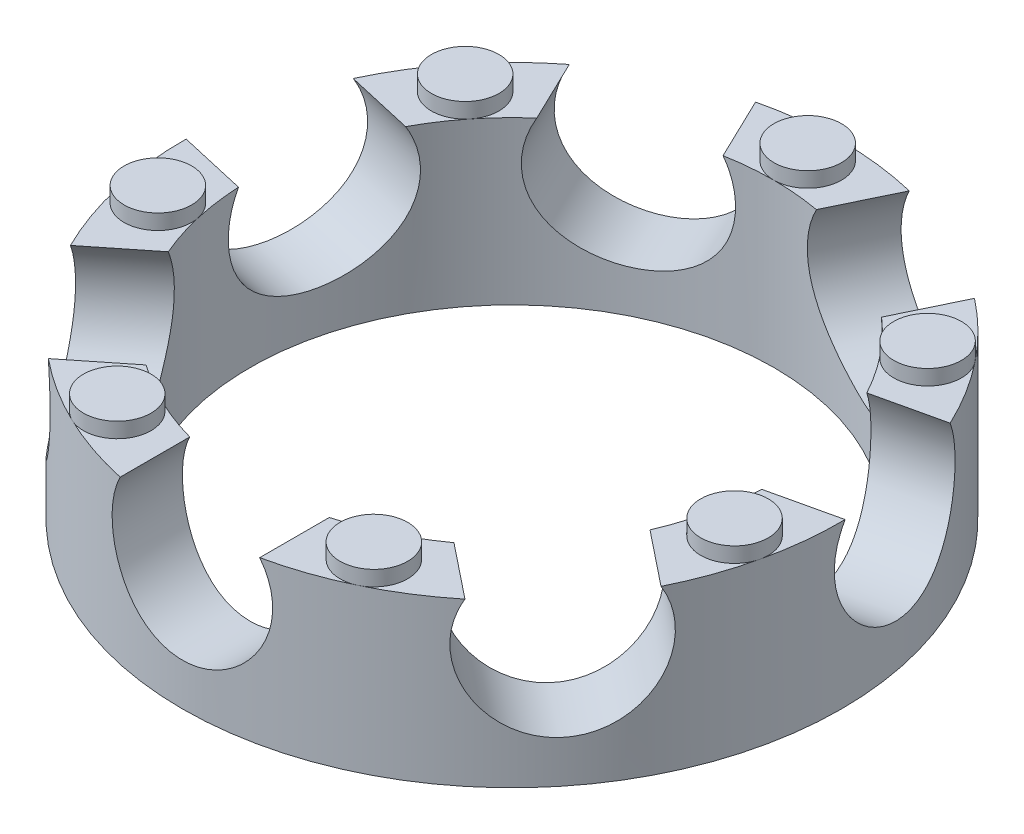
SolidWorks part; units mm, degrees
material "ABS"
ref_plane "Front Plane" through (0, 0, 0) normal (0, 0, 1) x (1, 0, 0)
ref_plane "Top Plane" through (0, 0, 0) normal (0, 1, 0) x (1, 0, 0)
ref_plane "Right Plane" through (0, 0, 0) normal (1, 0, 0) x (0, 0, -1)
sketch "Sketch1" plane through (0, 0, 0) normal (0, 1, 0) x (1, 0, 0)
  circle A0 centre (0, 0) radius 4.953
  dimension "D1" = 9.906
extrude "Boss-Extrude1" add sketch "Sketch1" along normal blind 2.4384
sketch "Sketch2" plane through (0, 2.4384, 0) normal (0, 1, 0) x (1, 0, 0)
  circle A0 centre (0, 0) radius 3.937
  dimension "D1" = 7.874
extrude "Cut-Extrude1" cut sketch "Sketch2" against normal blind 2.4384
sketch "Sketch3" plane through (0, 0, 0) normal (0, 1, 0) x (1, 0, 0)
  line L0 (0, 4.445) -> (0, 0) construction
  line L1 (0, 0) -> (3.4752, 2.7714) construction
  circle A0 centre (0, 4.445) radius 0.508
  circle A1 centre (0, 0) radius 4.953 construction
  circle A2 centre (0, 0) radius 3.937 construction
  circle A3 centre (3.4752, 2.7714) radius 0.508
  circle A4 centre (4.3336, -0.9891) radius 0.508
  circle A5 centre (1.9286, -4.0048) radius 0.508
  circle A6 centre (-1.9286, -4.0048) radius 0.508
  circle A7 centre (-4.3336, -0.9891) radius 0.508
  circle A8 centre (-3.4752, 2.7714) radius 0.508
  point P21 (0, 0)
  dimension "D1" = 51.429
  dimension "D2" = 7
extrude "Boss-Extrude2" add sketch "Sketch3" along normal blind 2.667
sketch "Sketch4" plane through (0, 0, 0) normal (0, 0, 1) x (1, 0, 0)
  line L0 (-4.953, 0) -> (4.953, 0) construction
  circle A0 centre (0, 1.8415) radius 1.2065
  dimension "D1" = 0.635
  dimension "D2" = 2.413
extrude "Cut-Extrude2" cut sketch "Sketch4" along normal up to surface (4.8038 mm away)
sketch "Sketch5" plane through (0, 0, 0) normal (0, 0, 1) x (1, 0, 0)
  line L0 (0, 0) -> (0, 2.667) construction
  line L1 (0.508, 2.667) -> (-0.508, 2.667) construction
pattern_circular "CirPattern1" count 7 over 360 of "Cut-Extrude2"
ref_plane "Plane1" through (0, 1.5367, 0) normal (0, 1, 0) x (1, 0, 0)
sketch "Sketch6" plane through (0, 1.5367, 0) normal (0, 1, 0) x (1, 0, 0)
  circle A0 centre (0, 0) radius 4.445 construction
